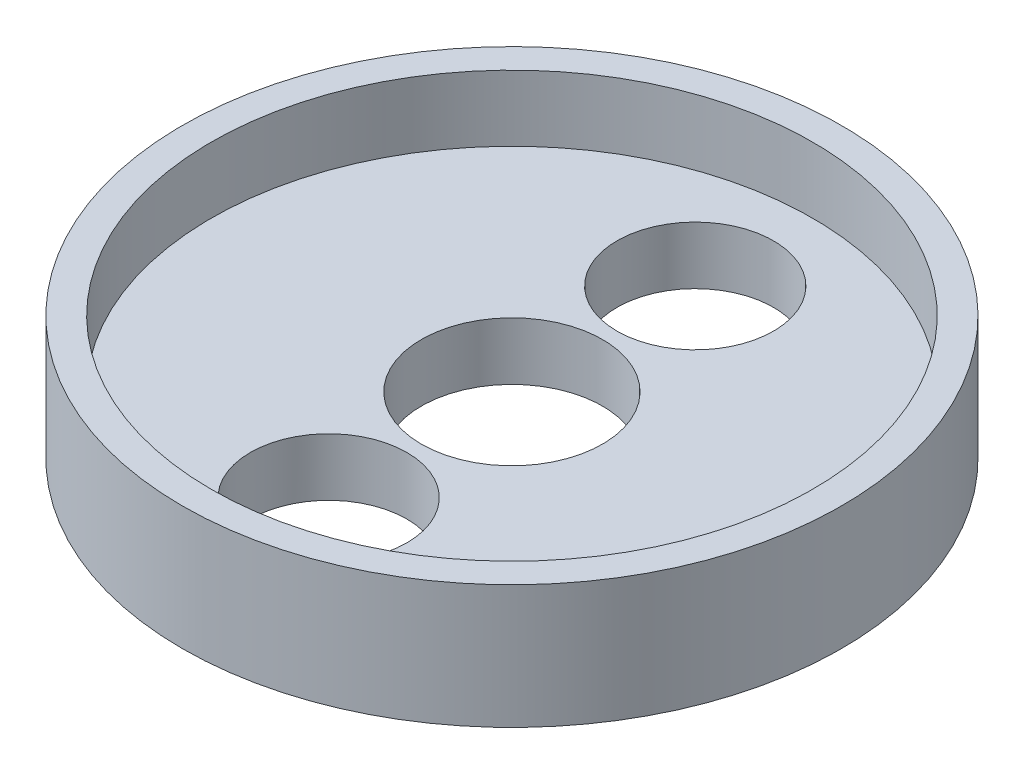
SolidWorks part; units mm, degrees
ref_plane "Front Plane" through (0, 0, 0) normal (0, 0, 1) x (1, 0, 0)
ref_plane "Top Plane" through (0, 0, 0) normal (0, 1, 0) x (1, 0, 0)
ref_plane "Right Plane" through (0, 0, 0) normal (1, 0, 0) x (0, 0, -1)
sketch "Sketch4" plane through (0, 0, 0) normal (0, 1, 0) x (1, 0, 0)
  line L0 (0, 5.5) -> (0, 11.125) construction
  line L1 (-5.5, 0) -> (5.5, 0) construction
  circle A1 centre (0, 0) radius 20
  circle A6 centre (0, 0) radius 5.5 construction
  circle A7 centre (0, 0) radius 5.5
  circle A8 centre (0, 11.125) radius 4.75
  circle A9 centre (0, -11.125) radius 4.75
  dimension "D1" = 11
  dimension "D2" = 40
  dimension "D4" = 5.625
  dimension "D3" = 9.5
extrude "LidBase" add sketch "Sketch4" along normal blind 7.5
sketch "Sketch5" plane through (0, 7.5, 0) normal (0, 1, 0) x (1, 0, 0)
  circle A1 centre (0, 0) radius 18.25
  dimension "D1" = 36.5
extrude "LidGrooves" cut sketch "Sketch5" against normal blind 4
